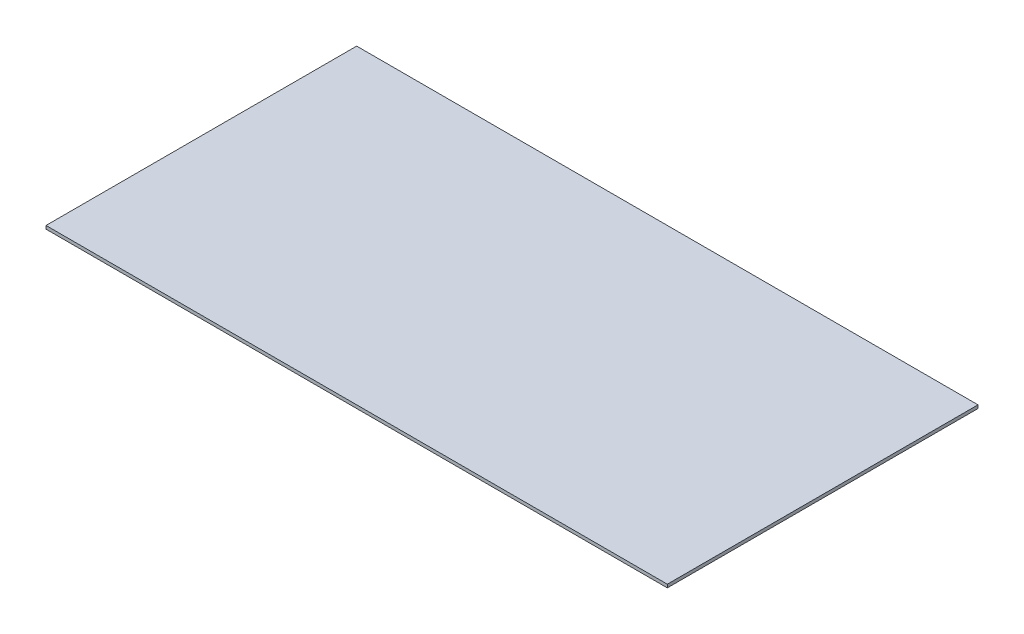
SolidWorks part; units mm, degrees
material "Maple"
ref_plane "Front Plane" through (0, 0, 0) normal (0, 0, 1) x (1, 0, 0)
ref_plane "Top Plane" through (0, 0, 0) normal (0, 1, 0) x (1, 0, 0)
ref_plane "Right Plane" through (0, 0, 0) normal (1, 0, 0) x (0, 0, -1)
sketch "Sketch1" plane through (0, 0, 0) normal (0, 1, 0) x (1, 0, 0)
  line L1 (0, 0) -> (2438.4, 0)
  line L2 (0, 0) -> (0, 1219.2)
  line L3 (0, 1219.2) -> (2438.4, 1219.2)
  line L4 (2438.4, 0) -> (2438.4, 1219.2)
  dimension "D1" = 1219.2
  dimension "D2" = 2438.4
extrude "Boss-Extrude1" add sketch "Sketch1" along normal blind 12.7
